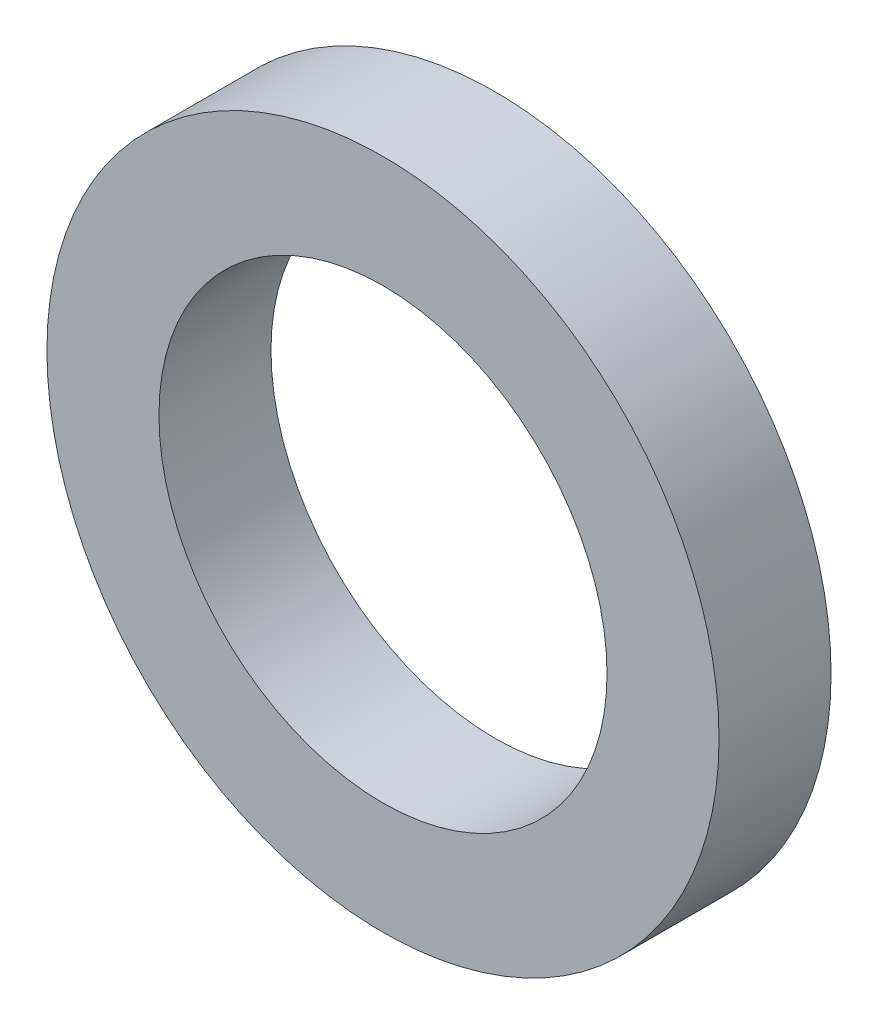
SolidWorks part; units mm, degrees
ref_plane "Plan de face" through (0, 0, 0) normal (0, 0, 1) x (1, 0, 0)
ref_plane "Plan de dessus" through (0, 0, 0) normal (0, 1, 0) x (1, 0, 0)
ref_plane "Plan de droite" through (0, 0, 0) normal (1, 0, 0) x (0, 0, -1)
sketch "Esquisse1" plane through (0, 0, 0) normal (0, 0, 1) x (1, 0, 0)
  circle A0 centre (0, 0) radius 4
  circle A1 centre (0, 0) radius 6
extrude "Extrusion1" add sketch "Esquisse1" along normal blind 2
